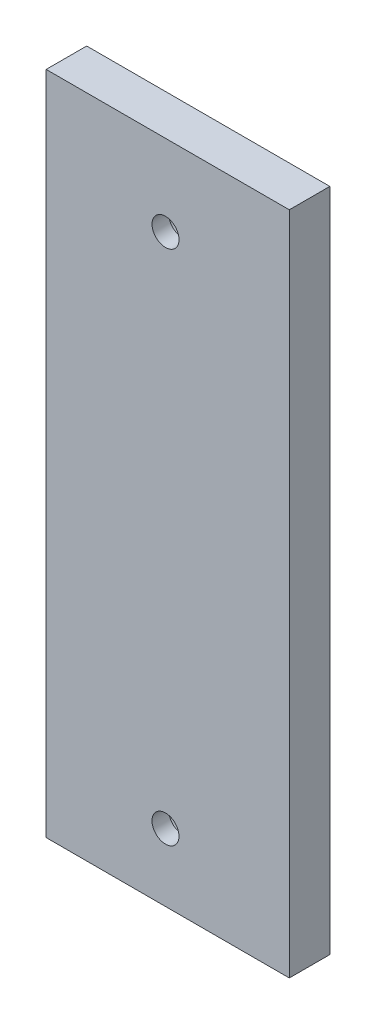
SolidWorks part; units mm, degrees
ref_plane "Front Plane" through (0, 0, 0) normal (0, 0, 1) x (1, 0, 0)
ref_plane "Top Plane" through (0, 0, 0) normal (0, 1, 0) x (1, 0, 0)
ref_plane "Right Plane" through (0, 0, 0) normal (1, 0, 0) x (0, 0, -1)
sketch "Sketch1" plane through (0, 0, 0) normal (0, 0, 1) x (1, 0, 0)
  line L0 (0.3302, 21.8284) -> (0.3302, 48.4943) construction
  line L1 (-19.6698, 10) -> (20.3302, 10)
  line L2 (-19.6698, 10) -> (-19.6698, -86.5)
  line L3 (-19.6698, -86.5) -> (20.3302, -86.5)
  line L4 (20.3302, 10) -> (20.3302, -86.5)
  line L5 (-12, 10) -> (12, 10) construction
  line L6 (-12, -86.5) -> (12, -86.5) construction
  dimension "D1" = 20
  dimension "D2" = 20
  dimension "D3" = 0
  dimension "D4" = 0
extrude "Boss-Extrude1" add sketch "Sketch1" along normal blind 4
sketch "Sketch3" plane through (0, -86.5, 0) normal (0, -1, 0) x (1, 0, 0)
  line L11 (-10.6141, -0.1) -> (-7.7586, -0.1)
  line L12 (-12.2482, 4.3897) -> (-7.7586, -0.1)
  line L13 (-10.6141, -0.1) -> (-12.2482, 4.3897)
  line L14 (7.7586, -0.1) -> (12.2482, 4.3897)
  line L15 (12.2482, 4.3897) -> (10.6141, -0.1)
  line L16 (7.7586, -0.1) -> (10.6141, -0.1)
  line M1 (-19.6698, 0) -> (20.3302, 0)
  line M3 (20.3302, 4) -> (-19.6698, 4)
extrude "Cut-Extrude3" cut sketch "Sketch3" against normal blind 20 contours L13 L12 M1 M3 | L15 L14 M3 M1
sketch "Sketch4" plane through (0, 10, 0) normal (0, 1, 0) x (1, 0, 0)
  line L0 (7.8586, 0) -> (11.8586, -4) construction
  line L1 (12.1064, -4) -> (10.6505, 0) construction
  line L2 (-43, 0) -> (43, 0) construction
  line L3 (-10.6505, 0) -> (-12.1064, -4) construction
  line L4 (-11.8586, -4) -> (-7.8586, 0) construction
  line L5 (7.8586, 0) -> (11.8586, -4)
  line L6 (12.1064, -4) -> (10.6505, 0)
  line L7 (-10.6505, 0) -> (-7.8586, 0)
  line L8 (-10.6505, 0) -> (-12.1064, -4)
  line L9 (-11.8586, -4) -> (-7.8586, 0)
  line L10 (7.8586, 0) -> (10.6505, 0)
  line L11 (-12.1064, -4) -> (-11.8586, -4)
  line L12 (11.8586, -4) -> (12.1064, -4)
  line M1 (20.3302, 0) -> (-19.6698, 0)
  line M3 (-19.6698, -4) -> (20.3302, -4)
sketch "Sketch5" plane through (0, 0, 4) normal (0, 0, 1) x (1, 0, 0)
  circle A0 centre (0, 0) radius 2
  circle A1 centre (0, -76.5) radius 2
  dimension "D1" = 4
  dimension "D2" = 4
extrude "Cut-Extrude5" cut sketch "Sketch5" against normal blind 10
sketch "Sketch6" plane through (0, 0, 4) normal (0, 0, 1) x (1, 0, 0)
  line L0 (20.3302, 10) -> (-19.6698, 10) construction
  line L1 (-19.6698, -86.5) -> (-17.6698, -86.5)
  line L2 (-19.6698, -86.5) -> (-19.6698, 10)
  line L3 (-19.6698, 10) -> (-17.6698, 10)
  line L4 (-17.6698, -86.5) -> (-17.6698, 10)
  line L5 (12.1064, -86.5) -> (20.3302, -86.5) construction
  line L6 (20.3302, 10) -> (18.3302, 10)
  line L7 (20.3302, 10) -> (20.3302, -86.5)
  line L8 (20.3302, -86.5) -> (18.3302, -86.5)
  line L9 (18.3302, 10) -> (18.3302, -86.5)
  dimension "D1" = 2
  dimension "D2" = 2
extrude "Cut-Extrude6" cut sketch "Sketch6" against normal blind 10
sketch "Sketch7" plane through (0, 0, 4) normal (0, 0, 1) x (1, 0, 0)
  line L1 (-17.6698, 10) -> (18.3302, 10)
  line L2 (-17.6698, 10) -> (-17.6698, -86.5)
  line L3 (-17.6698, -86.5) -> (18.3302, -86.5)
  line L4 (18.3302, 10) -> (18.3302, -86.5)
  circle A0 centre (0, -76.5) radius 2 construction
  circle A1 centre (0, 0) radius 2 construction
  circle A2 centre (0, -76.5) radius 2
  circle A3 centre (0, 0) radius 2
extrude "Boss-Extrude2" add sketch "Sketch7" along normal blind 2
extrude "Cut-Extrude7" cut sketch "Sketch4" against normal through all contours L9 L8 M3 M1 | L6 L5 M3 M1
sketch "Sketch8" plane through (0, 0, 0) normal (0, 0, -1) x (-1, 0, 0)
  circle A0 centre (0, 0) radius 4.25
  circle A1 centre (0, -76.5) radius 4.25
  circle A2 centre (0, -76.5) radius 2 construction
  circle A3 centre (0, 0) radius 2 construction
  circle A4 centre (0, -76.5) radius 2
  circle A5 centre (0, 0) radius 2
  circle M4 centre (0, -76.5) radius 2
  circle M5 centre (0, 0) radius 2
  dimension "D1" = 8.5
extrude "Cut-Extrude8" cut sketch "Sketch8" against normal blind 3.5 contours A0 M5 | A1 M4
sketch "Sketch9" plane through (0, 10, 0) normal (0, 1, 0) x (1, 0, 0)
  line L14 (-10.7906, 0.2) -> (-7.3757, 0.2)
  line L15 (-11.7757, -4.2) -> (-7.3757, 0.2)
  line L16 (-12.392, -4.2) -> (-11.7757, -4.2)
  line L17 (-10.7906, 0.2) -> (-12.392, -4.2)
  line L18 (7.3757, 0.2) -> (10.7906, 0.2)
  line L19 (12.392, -4.2) -> (10.7906, 0.2)
  line L20 (11.7757, -4.2) -> (12.392, -4.2)
  line L21 (7.3757, 0.2) -> (11.7757, -4.2)
extrude "Cut-Extrude10" cut sketch "Sketch9" against normal blind 122
sketch "Sketch10" plane through (0, 10, 0) normal (0, 1, 0) x (1, 0, 0)
  line L1 (-17.6698, 0) -> (18.3302, 0)
  line L2 (-17.6698, 0) -> (-17.6698, -6)
  line L3 (-17.6698, -6) -> (18.3302, -6)
  line L4 (18.3302, 0) -> (18.3302, -6)
extrude "Boss-Extrude3" add sketch "Sketch10" along normal blind 2
